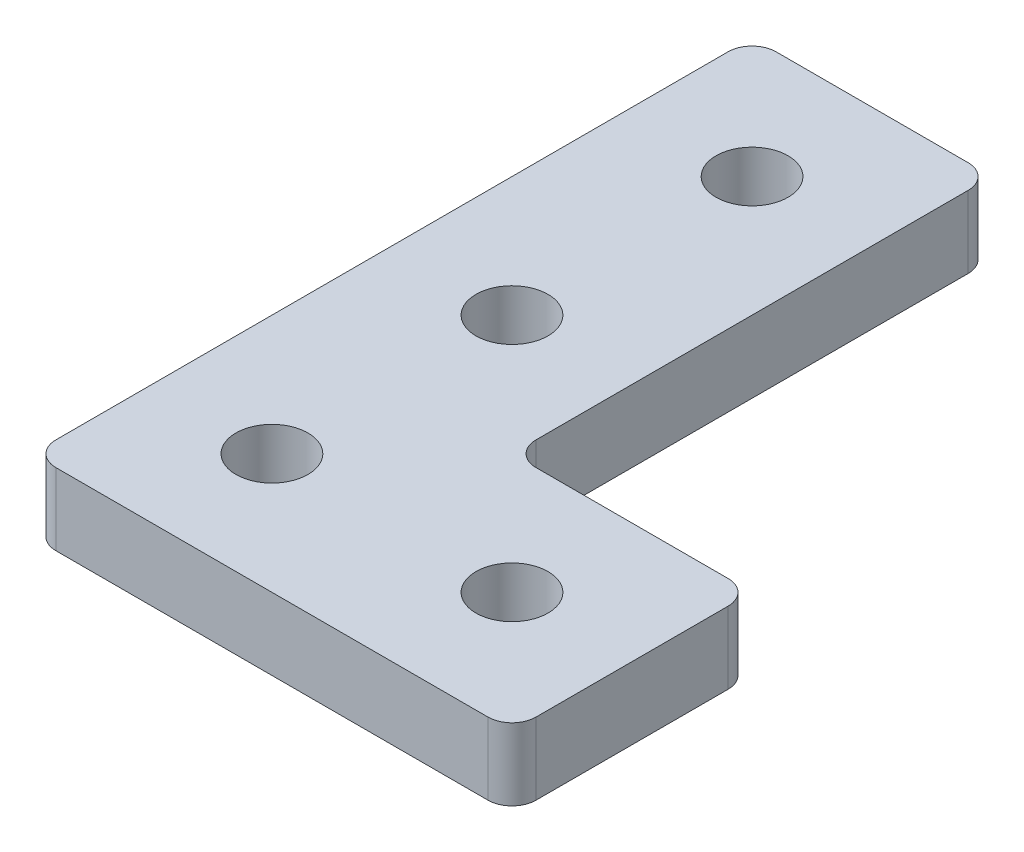
SolidWorks part; units mm, degrees
ref_plane "Front Plane" through (0, 0, 0) normal (0, 0, 1) x (1, 0, 0)
ref_plane "Top Plane" through (0, 0, 0) normal (0, 1, 0) x (1, 0, 0)
ref_plane "Right Plane" through (0, 0, 0) normal (1, 0, 0) x (0, 0, -1)
sketch "Sketch1" plane through (0, 0, 0) normal (0, 1, 0) x (1, 0, 0)
  line L1 (0, 0) -> (10, 0)
  line L2 (0, 0) -> (0, 30)
  line L3 (0, 30) -> (10, 30)
  line L4 (10, 10) -> (10, 30)
  line L5 (10, 0) -> (20, 0)
  line L7 (10, 10) -> (20, 10)
  line L8 (20, 0) -> (20, 10)
  circle A0 centre (5, 25) radius 1.5
  circle A1 centre (5, 15) radius 1.5
  circle A2 centre (5, 5) radius 1.5
  circle A3 centre (15, 5) radius 1.5
  point P10 (5, 30)
  dimension "D5" = 3
  dimension "D1" = 10
  dimension "D2" = 10
  dimension "D3" = 10
  dimension "D4" = 30
  dimension "D6" = 5
  dimension "D7" = 3
  dimension "D8" = 2
extrude "Boss-Extrude1" add sketch "Sketch1" along normal blind 3
fillet "Fillet1" radius 1 1 edges at (10, 1.5, -10)
fillet "Fillet2" radius 1 5 edges at (0, 1.5, -30) (10, 1.5, -30) (0, 1.5, 0) (20, 1.5, 0) (20, 1.5, -10)
